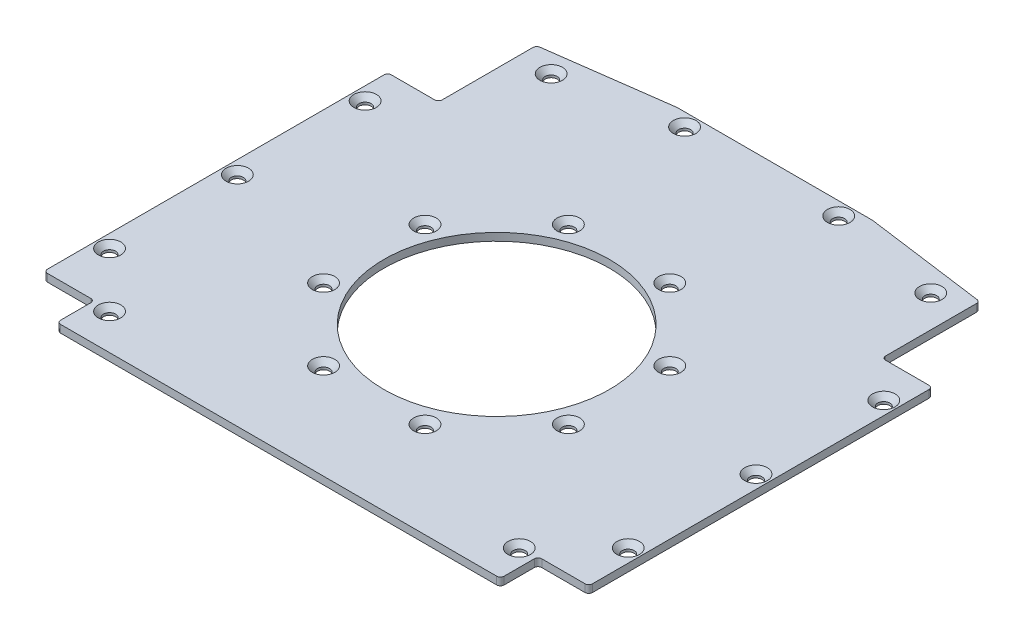
SolidWorks part; units mm, degrees
material "7075-T6, Plate (SS)"
ref_plane "Front Plane" through (0, 0, 0) normal (0, 0, 1) x (1, 0, 0)
ref_plane "Top Plane" through (0, 0, 0) normal (0, 1, 0) x (1, 0, 0)
ref_plane "Right Plane" through (0, 0, 0) normal (1, 0, 0) x (0, 0, -1)
sketch "Sketch1" plane through (0, 0, 0) normal (0, 1, 0) x (1, 0, 0)
  line L0 (0, 0) -> (0, 74) construction
  line L1 (-72.5, -58) -> (72.5, -58)
  line L2 (-72.5, -58) -> (-72.5, 74)
  line L3 (-72.5, 74) -> (72.5, 74)
  line L4 (72.5, -58) -> (72.5, 74)
  circle A0 centre (0, 0) radius 30
  point P0 (0, 0)
  dimension "D3" = 60
  dimension "D1" = 58
  dimension "D2" = 145
  dimension "D4" = 74
extrude "Boss-Extrude1" add sketch "Sketch1" along normal blind 2.032
hole_wizard "CSK for M3 SFHCS1" positions "Sketch3" profile "Sketch2" countersink size "M3" standard "ANSI Metric" end condition through all
sketch "Sketch3" plane through (-52.5563, 2.032, -0.4264) normal (0, -1, 0) x (-1, 0, 0)
  line L0 (-52.5563, -0.4264) -> (-52.5563, 20.0218) construction
  line L2 (-52.5563, -0.4264) -> (-39.0667, 32.1404) construction
  point P0 (-66.0459, -32.9931)
  point P8 (-85.1231, -13.916)
  point P9 (-85.1231, 13.0632)
  point P10 (-66.0459, 32.1404)
  point P11 (-39.0667, 32.1404)
  point P12 (-19.9896, 13.0632)
  point P13 (-19.9896, -13.916)
  point P14 (-39.0667, -32.9931)
  dimension "D1" = 35.25
  dimension "D3" = 35.25
  dimension "D4" = 22.5
  dimension "D2" = 8
sketch "Sketch2" plane through (13.4896, 2.032, 32.5668) normal (1, 0, 0) x (0, 0, 1)
  line L0 (0, 0) -> (0, 2.032)
  line L1 (0, 2.032) -> (1.6, 2.032)
  line L2 (1.6, 2.032) -> (1.6, 1.4)
  line L3 (1.6, 1.4) -> (3, 0)
  line L5 (3, 0) -> (0, 0)
  line L6 (-1.6, 1.4) -> (-3, 0) construction
  line L11 (0, -6.35) -> (0, 107.95) construction
  dimension "Thru Hole Dia." = 3.2
  dimension "Thru Hole Depth" = 2.032
  dimension "Near C'Sink Dia." = 6
  dimension "Near C'Sink Angle" = 90
hole_wizard "CSK for M3 SFHCS2" positions "Sketch7" profile "Sketch5" countersink size "M3" standard "ANSI Metric" end condition through all
sketch "Sketch7" plane through (0, 2.032, 0) normal (0, 1, 0) x (1, 0, 0)
  line L1 (63.6346, 0) -> (0, 0) construction
  line L2 (0, 0) -> (0, -114.1553) construction
  circle A1 centre (-69, -34) radius 1.25 construction
  circle A3 centre (-54.5, -48.5) radius 1.25 construction
  circle A4 centre (-69, 0) radius 1.25 construction
  circle A5 centre (-50.5, 65) radius 1.25 construction
  circle A6 centre (-20.5, 70.5) radius 1.25 construction
  point P5 (-69, -34)
  point P9 (-54.5, -48.5)
  point P11 (-69, 0)
  point P35 (69, 0)
  point P36 (54.5, -48.5)
  point P38 (69, -34)
  point P41 (69, 34)
  point P48 (-69, 34)
  point P52 (-50.5, 65)
  point P54 (-20.5, 70.5)
  point P68 (20.5, 70.5)
  point P69 (50.5, 65)
sketch "Sketch5" plane through (-69, 2.032, 34) normal (1, 0, 0) x (0, 0, 1)
  line L0 (0, 0) -> (0, 2.032)
  line L1 (0, 2.032) -> (1.6, 2.032)
  line L2 (1.6, 2.032) -> (1.6, 1.4)
  line L3 (1.6, 1.4) -> (3, 0)
  line L5 (3, 0) -> (0, 0)
  line L6 (-1.6, 1.4) -> (-3, 0) construction
  line L11 (0, -6.35) -> (0, 107.95) construction
  dimension "Thru Hole Dia." = 3.2
  dimension "Thru Hole Depth" = 2.032
  dimension "Near C'Sink Dia." = 6
  dimension "Near C'Sink Angle" = 90
sketch "Sketch9" plane through (0, 2.032, 0) normal (0, 1, 0) x (1, 0, 0)
  line L0 (-72.5, -48) -> (-59, -48)
  line L3 (-59, -48) -> (-59, -58)
  line L4 (-59, -59.5) -> (-59, -39.5) construction
  line L6 (-72.5, 74) -> (-72.5, -58) construction
  line L7 (-72.5, -58) -> (72.5, -58) construction
  line L8 (-72.5, -48) -> (-72.5, -58)
  line L9 (-72.5, -58) -> (-59, -58)
  line L10 (0, 0) -> (0, -37.6505) construction
  line L11 (72.5, -58) -> (59, -58)
  line L12 (72.5, -48) -> (72.5, -58)
  line L13 (59, -48) -> (59, -58)
  line L14 (72.5, -48) -> (59, -48)
  line L15 (-26, 74) -> (-59, 69.5286)
  line L16 (72.5, 74) -> (-72.5, 74) construction
  line L17 (-74.4399, 67.4366) -> (-26, 74) construction
  line L18 (-59, 69.5286) -> (-59, 43.5)
  line L19 (-59, 43.5) -> (-72.5, 43.5)
  line L20 (-59, 39.5) -> (-59, 60.5) construction
  line L21 (-60, 61.5) -> (-73.5, 61.5) construction
  line L22 (-26, 74) -> (-72.5, 74)
  line L23 (-72.5, 74) -> (-72.5, 43.5)
  line L24 (72.5, 74) -> (72.5, 43.5)
  line L25 (26, 74) -> (72.5, 74)
  line L26 (59, 43.5) -> (72.5, 43.5)
  line L27 (59, 69.5286) -> (59, 43.5)
  line L28 (26, 74) -> (59, 69.5286)
  dimension "D1" = 10
  dimension "D2" = 18
extrude "Cut-Extrude3" cut sketch "Sketch9" against normal through all
fillet "Fillet1" radius 1 12 edges at (-59, 1.016, 48) (-72.5, 1.016, 48) (-59, 1.016, 58) (59, 1.016, 58) (59, 1.016, 48) (72.5, 1.016, 48) (72.5, 1.016, -43.5) (59, 1.016, -43.5) (59, 1.016, -69.5286) (-59, 1.016, -69.5286) (-72.5, 1.016, -43.5) (-59, 1.016, -43.5)
